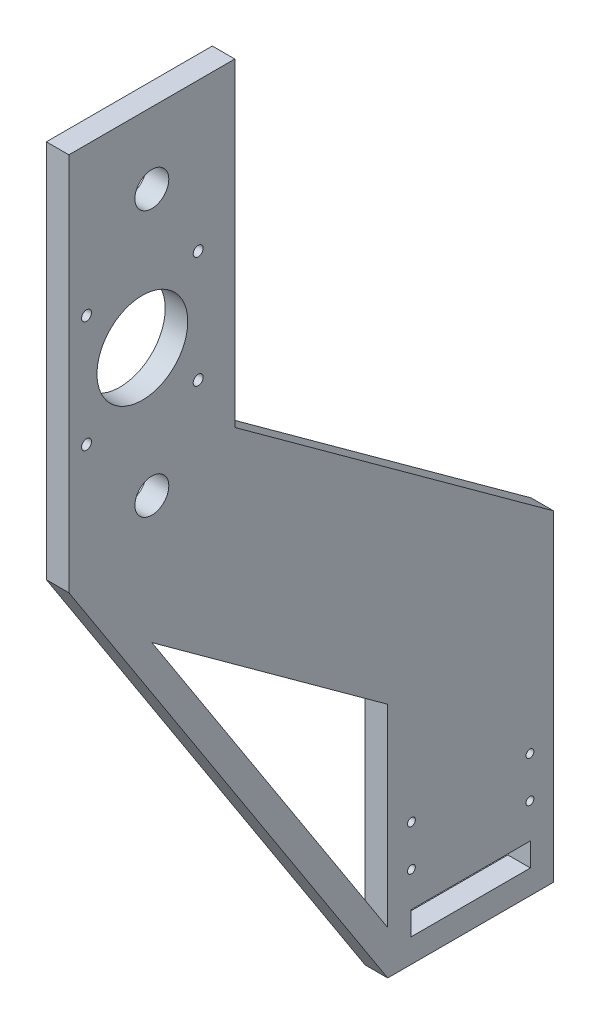
SolidWorks part; units mm, degrees
ref_plane "Front Plane" through (0, 0, 0) normal (0, 0, 1) x (1, 0, 0)
ref_plane "Top Plane" through (0, 0, 0) normal (0, 1, 0) x (1, 0, 0)
ref_plane "Right Plane" through (0, 0, 0) normal (1, 0, 0) x (0, 0, -1)
sketch "Sketch1" plane through (0, 0, 0) normal (1, 0, 0) x (0, 0, -1)
  line L0 (0, 0) -> (70, 0)
  line L1 (70, 0) -> (70, 135.6671)
  line L2 (70, 135.6671) -> (-64.5, 233.3855)
  line L3 (-64.5, 233.3855) -> (-64.5, 368)
  line L4 (-64.5, 368) -> (-134.5, 368)
  line L5 (-134.5, 368) -> (-134.5, 208)
  line L6 (-99.5, 172.2898) -> (0, 100)
  line L7 (0, 100) -> (0, 18.4162)
  line L8 (-99.5, 368) -> (-99.5, 172.2898) construction
  line L9 (-103.5, 282) -> (-84.35, 282) construction
  line L10 (-103.5, 282) -> (-103.5, 301.15) construction
  line L11 (-134.5, 208) -> (0, 0)
  line L12 (9.8, 20) -> (60.2, 20)
  line L13 (9.8, 20) -> (9.8, 10.1)
  line L14 (9.8, 10.1) -> (60.2, 10.1)
  line L15 (60.2, 20) -> (60.2, 10.1)
  line L16 (0, 18.4162) -> (-99.5, 172.2898)
  circle A0 centre (-99.5, 338) radius 7.15
  circle A1 centre (-99.5, 226) radius 7.15
  circle A2 centre (-103.5, 282) radius 19.15
  point P19 (35, 10.1)
  point P20 (35, 0)
  dimension "D8" = 14.3
  dimension "D9" = 4
  dimension "D10" = 38.3
  dimension "D11" = 50.4
  dimension "D12" = 20
  dimension "D15" = 30
  dimension "D16" = 112
  dimension "D19" = 10
  dimension "D2" = 368
  dimension "D3" = 160
  dimension "D4" = 100
  dimension "D5" = 70
  dimension "D6" = 70
  dimension "D7" = 204.5
  dimension "D18" = 9.9
  dimension "70" = 70
extrude "Boss-Extrude1" add sketch "Sketch1" along normal blind 9.5
hole_wizard "M4 Tapped Hole1" positions "Sketch2" profile "Sketch3" tap size "M4" standard "ISO" end condition through all
sketch "Sketch2" plane through (9.5, 0, 0) normal (1, 0, 0) x (0, 0, -1)
  line L0 (35, 0) -> (35, 161.0957) construction
  line L4 (60.2, 20) -> (9.8, 20) construction
  line L5 (0, 0) -> (70, 0) construction
  line L6 (70, 135.6671) -> (-64.5, 233.3855) construction
  point P0 (10, 34.7)
  point P2 (10, 52)
  point P17 (60, 52)
  point P18 (60, 34.7)
  dimension "D1" = 14.7
  dimension "D2" = 17.3
  dimension "D3" = 50
sketch "Sketch3" plane through (9.5, 34.7, -10) normal (0, 1, 0) x (0, 0, -1)
  line L0 (0, 0) -> (0, 9.5)
  line L1 (0, 9.5) -> (1.65, 9.5)
  line L2 (1.65, 9.5) -> (1.65, 0)
  line L5 (1.65, 0) -> (0, 0)
  line L11 (0, -6.35) -> (0, 107.95) construction
  dimension "Thru Tap Drill Dia." = 3.3
  dimension "Thru Tap Drill Depth" = 9.5
cosmetic thread "Hole Thread1" parameters "D2"=4
cosmetic thread "Hole Thread2" parameters "D2"=4
cosmetic thread "Hole Thread3" parameters "D2"=4
cosmetic thread "Hole Thread4" parameters "D2"=4
hole_wizard "M5 Tapped Hole2" positions "Sketch4" profile "Sketch5" tap size "M5" standard "ISO" end condition through all
sketch "Sketch4" plane through (9.5, 0, 0) normal (1, 0, 0) x (0, 0, -1)
  circle A0 centre (-103.5, 282) radius 19.15 construction
  point P0 (-127.05, 305.55)
  point P9 (-79.95, 305.55)
  point P10 (-79.95, 258.45)
  point P11 (-127.05, 258.45)
  dimension "D3" = 23.55
  dimension "D4" = 23.55
  dimension "D1" = 2
  dimension "D2" = 2
sketch "Sketch5" plane through (9.5, 305.55, 127.05) normal (0, 1, 0) x (0, 0, -1)
  line L0 (0, 0) -> (0, 9.5)
  line L1 (0, 9.5) -> (2.1, 9.5)
  line L2 (2.1, 9.5) -> (2.1, 0)
  line L5 (2.1, 0) -> (0, 0)
  line L11 (0, -6.35) -> (0, 107.95) construction
  dimension "Thru Tap Drill Dia." = 4.2
  dimension "Thru Tap Drill Depth" = 9.5
cosmetic thread "Hole Thread9" parameters "D2"=5
cosmetic thread "Hole Thread10" parameters "D2"=5
cosmetic thread "Hole Thread11" parameters "D2"=5
cosmetic thread "Hole Thread12" parameters "D2"=5
